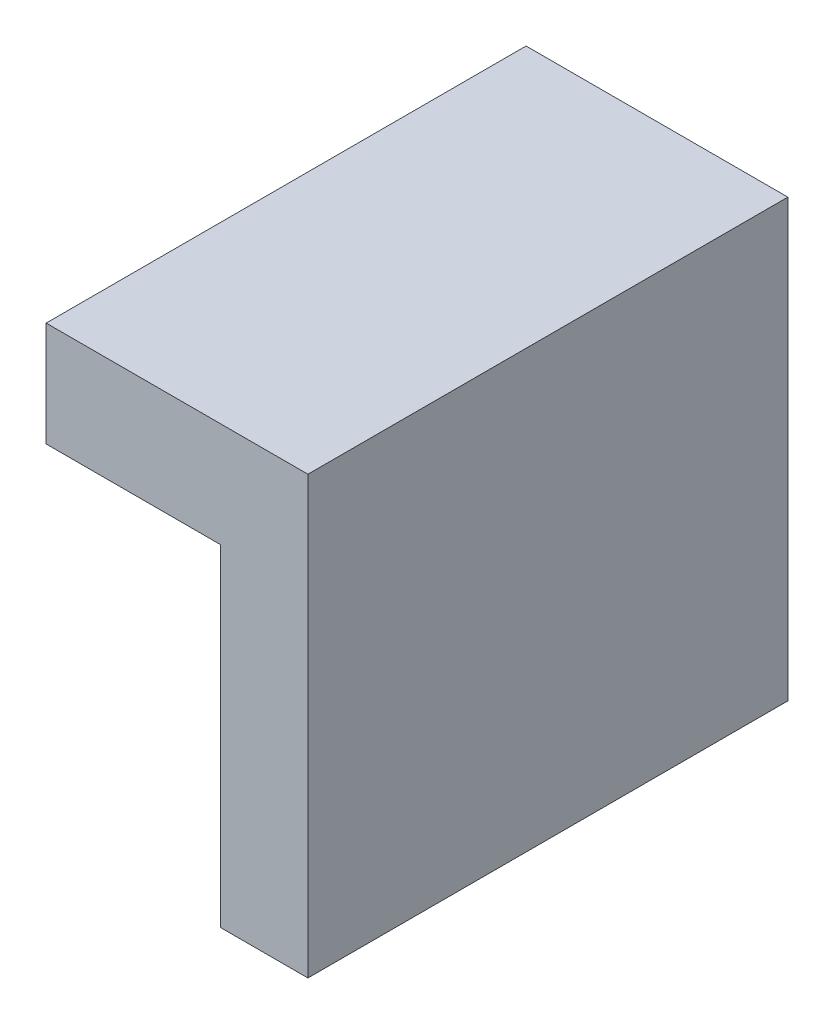
SolidWorks part; units mm, degrees
material "Wrought Stainless Steel"
ref_plane "Front Plane" through (0, 0, 0) normal (0, 0, 1) x (1, 0, 0)
ref_plane "Top Plane" through (0, 0, 0) normal (0, 1, 0) x (1, 0, 0)
ref_plane "Right Plane" through (0, 0, 0) normal (1, 0, 0) x (0, 0, -1)
sketch "Sketch1" plane through (0, 0, 0) normal (0, 0, 1) x (1, 0, 0)
  line L0 (-15, 20) -> (12, 20)
  line L1 (-15, -25) -> (15, -25)
  line L2 (-15, -25) -> (-15, 25)
  line L3 (-15, 25) -> (15, 25)
  line L4 (15, -25) -> (15, 25)
  line L5 (-15, -25) -> (15, 25) construction
  line L6 (-15, 25) -> (15, -25) construction
  line L7 (12, 20) -> (12, -25)
  line L8 (-15, 17) -> (9, 17)
  line L9 (9, 17) -> (9, -25)
  line L10 (-15, 13) -> (5, 13)
  line L11 (5, 13) -> (5, -25)
  point P0 (0, 0)
  dimension "D1" = 30
  dimension "D2" = 50
  dimension "D3" = 5
  dimension "D4" = 3
  dimension "D5" = 4
extrude "Boss-Extrude1" add sketch "Sketch1" along normal blind 55 contours L10 L11 L1 L9 L8 L2 | L0 L7 L1 L4 L3 L2
sketch "Sketch2" plane through (0, 0, 55) normal (0, 0, 1) x (1, 0, 0)
  line L1 (-15, 13) -> (15, 13)
  line L2 (-15, 13) -> (-15, 25)
  line L3 (-15, 25) -> (15, 25)
  line L4 (15, 13) -> (15, 25)
  line L5 (5, 13) -> (15, 13)
  line L6 (5, 13) -> (5, -25)
  line L7 (5, -25) -> (15, -25)
  line L8 (15, 13) -> (15, -25)
  line M1 (-15, 13) -> (5, 13)
  line M2 (5, 13) -> (5, -25)
  line M3 (5, -25) -> (9, -25)
  line M4 (9, -25) -> (9, 17)
  line M5 (9, 17) -> (-15, 17)
  line M6 (-15, 17) -> (-15, 13)
extrude "Boss-Extrude2" add sketch "Sketch2" against normal blind 5 contours L1 L4 L3 L2 M5 M4 | L1 M1 M4 M5 M6 | L1 M2 M3 M4 | L8 L1 L7 M4
sketch "Sketch3" plane through (0, 25, 0) normal (0, 1, 0) x (1, 0, 0)
  line L0 (-15, 0) -> (15, 0) construction
  line L1 (-15, -55) -> (15, -55) construction
  line L2 (-15, 0) -> (-15, -55) construction
  point P0 (0, -10)
  point P1 (0, -40)
  point P8 (0, 0)
  dimension "D1" = 10
  dimension "D2" = 15
  dimension "D3" = 15
  dimension "D4" = 15
sketch "Sketch4" plane through (15, 0, 0) normal (1, 0, 0) x (0, 0, -1)
  line L0 (-55, -25) -> (-55, 25) construction
  line L1 (0, -25) -> (0, 25) construction
  line L2 (0, 25) -> (-55, 25) construction
  point P0 (-40, 0)
  point P1 (-10, 0)
  dimension "D1" = 15
  dimension "D2" = 10
  dimension "D3" = 25
  dimension "D4" = 25
